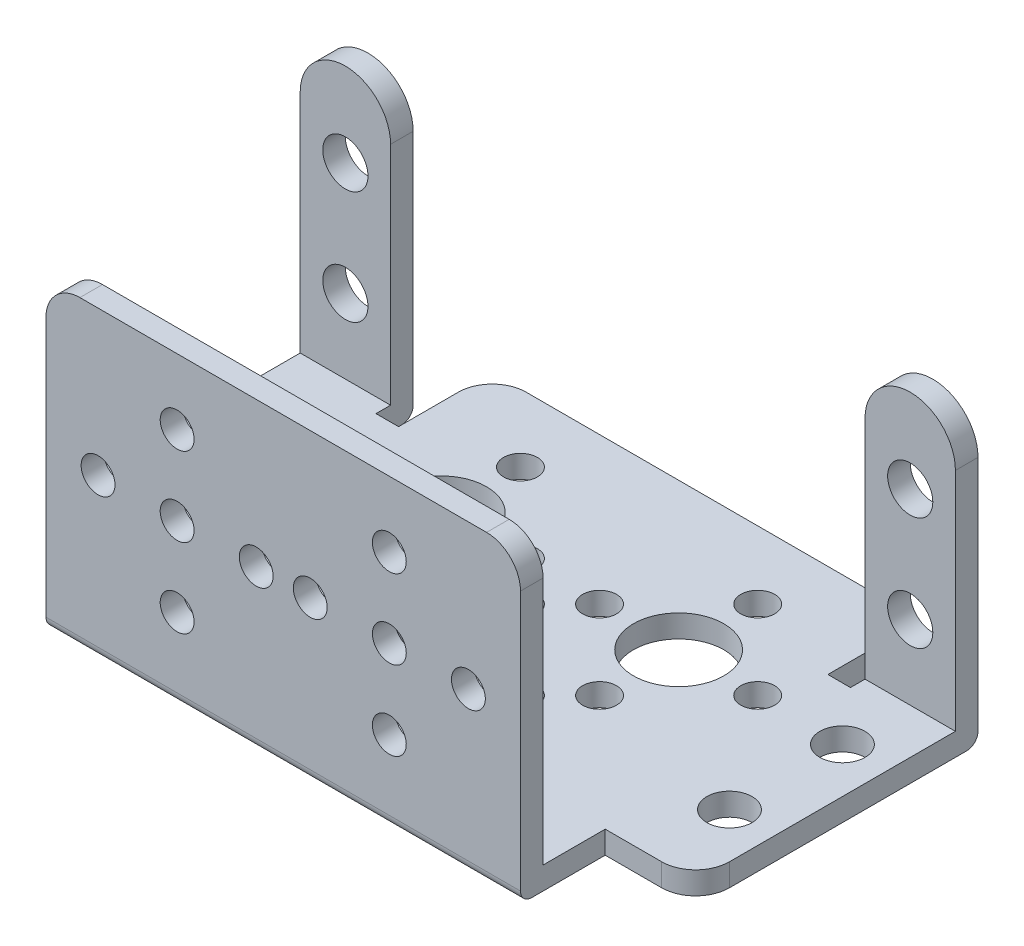
SolidWorks part; units mm, degrees
ref_plane "Front Plane" through (0, 0, 0) normal (0, 0, 1) x (1, 0, 0)
ref_plane "Top Plane" through (0, 0, 0) normal (0, 1, 0) x (1, 0, 0)
ref_plane "Right Plane" through (0, 0, 0) normal (1, 0, 0) x (0, 0, -1)
sketch "Sketch1" plane through (0, 0, 0) normal (0, 1, 0) x (1, 0, 0)
  line L0 (0, 0) -> (0, 35.8825) construction
  line L1 (21, 0) -> (-21, 0)
  line L2 (-21, 0) -> (-21, 7.5)
  line L3 (-21, 7.5) -> (-26, 7.5)
  line L4 (-29, 10.5) -> (-29, 32.5)
  line L5 (-29, 32.5) -> (-21, 32.5)
  line L6 (-21, 32.5) -> (-21, 29.2093)
  line L7 (-21, 29.2093) -> (-19, 29.2093)
  line L8 (-19, 29.2093) -> (-19, 34.5)
  line L9 (-16, 37.5) -> (16, 37.5)
  line L10 (21, 0) -> (21, 7.5)
  line L11 (21, 7.5) -> (26, 7.5)
  line L12 (19, 29.2093) -> (19, 34.5)
  line L13 (21, 29.2093) -> (19, 29.2093)
  line L14 (21, 32.5) -> (21, 29.2093)
  line L15 (29, 32.5) -> (21, 32.5)
  line L16 (29, 10.5) -> (29, 32.5)
  circle A0 centre (-25, 24.5) radius 2
  circle A1 centre (-25, 14.5) radius 2
  circle A2 centre (25, 14.5) radius 2
  circle A3 centre (25, 24.5) radius 2
  arc A4 (19, 34.5) -> (16, 37.5) centre (16, 34.5) ccw
  arc A5 (26, 7.5) -> (29, 10.5) centre (26, 10.5) ccw
  arc A6 (-19, 34.5) -> (-16, 37.5) centre (-16, 34.5) cw
  arc A7 (-26, 7.5) -> (-29, 10.5) centre (-26, 10.5) cw
  circle A8 centre (0, 14) radius 7 construction
  circle A9 centre (0, 14) radius 4
  circle A10 centre (0, 21) radius 1.5
  circle A11 centre (7, 14) radius 1.5
  circle A12 centre (0, 7) radius 1.5
  circle A13 centre (-7, 14) radius 1.5
  circle A14 centre (10.5, 24.5) radius 7 construction
  circle A15 centre (10.5, 24.5) radius 4
  circle A16 centre (10.5, 31.5) radius 1.5
  circle A20 centre (-10.5, 24.5) radius 7 construction
  circle A21 centre (-10.5, 24.5) radius 4
  circle A22 centre (-10.5, 31.5) radius 1.5
  circle A26 centre (3.5, 24.5) radius 1.5
  circle A27 centre (10.5, 17.5) radius 1.5
  circle A28 centre (17.5, 24.5) radius 1.5
  circle A29 centre (-3.5, 24.5) radius 1.5
  circle A30 centre (-10.5, 17.5) radius 1.5
  circle A31 centre (-17.5, 24.5) radius 1.5
  point P13 (0, 37.5)
  point P30 (19, 37.5)
  point P33 (29, 7.5)
  point P36 (-19, 37.5)
  point P39 (-29, 7.5)
  dimension "D6" = 4
  dimension "D7" = 4
  dimension "D8" = 10
  dimension "D9" = 14.5
  dimension "D11" = 3
  dimension "D12" = 14
  dimension "D13" = 8
  dimension "D14" = 3
  dimension "D16" = 14
  dimension "D17" = 8
  dimension "D18" = 3
  dimension "D19" = 14
  dimension "D20" = 8
  dimension "D21" = 3
  dimension "D24" = 21
  dimension "D26" = 14
  dimension "D1" = 38
  dimension "D2" = 58
  dimension "D3" = 37.5
  dimension "D4" = 32.5
  dimension "D5" = 2
  dimension "D10" = 7.5
  dimension "D25" = 10.5
  dimension "D15" = 4
  dimension "D22" = 4
  dimension "D23" = 4
extrude "Boss-Extrude1" add sketch "Sketch1" along normal blind 27
sketch "Sketch3" plane through (0, 0, 0) normal (1, 0, 0) x (0, 0, -1)
  line L0 (0, 27) -> (0, 0) construction
  line L1 (2, 28.5272) -> (30.5, 28.5272)
  line L2 (2, 28.5272) -> (2, 2)
  line L3 (2, 2) -> (30.5, 2)
  line L4 (30.5, 28.5272) -> (30.5, 2)
  line L5 (0, 0) -> (7.5, 0) construction
  line L7 (32.557, 2) -> (38.8255, 2)
  line L8 (32.557, 2) -> (32.557, 28.5272)
  line L9 (32.557, 28.5272) -> (38.8255, 28.5272)
  line L10 (38.8255, 2) -> (38.8255, 28.5272)
  dimension "D1" = 28.5
  dimension "D2" = 2
  dimension "D3" = 2
extrude "Cut-Extrude1" cut sketch "Sketch3" against normal through all both and the other way through all
sketch "Sketch4" plane through (0, 0, 0) normal (0, 0, 1) x (1, 0, 0)
  line L0 (-21, 27) -> (-21, 2) construction
  line L1 (-29, 0) -> (-21, 0) construction
  line L2 (-29, 0) -> (-29, 26) construction
  line L3 (-29, 26) -> (-21, 26) construction
  line L4 (-21, 0) -> (-21, 26) construction
  line L5 (0, 0) -> (0, 14.6606) construction
  line L6 (29, 0) -> (21, 0) construction
  line L7 (21, 0) -> (21, 26) construction
  line L8 (29, 0) -> (29, 26) construction
  line L9 (29, 26) -> (21, 26) construction
  line L10 (-29, 22) -> (-29, 28.588)
  line L11 (-29, 28.588) -> (-21, 28.588)
  line L12 (-21, 28.588) -> (-21, 22)
  line L14 (29, 26) -> (21, 26) construction
  line L16 (21, 28.588) -> (21, 22)
  line L17 (29, 28.588) -> (21, 28.588)
  line L18 (29, 22) -> (29, 28.588)
  arc A0 (-21, 22) -> (-29, 22) centre (-25, 22) ccw
  arc A1 (21, 22) -> (29, 22) centre (25, 22) cw
  circle A2 centre (-25, 18.5734) radius 2
  circle A3 centre (-25, 8.5734) radius 2
  circle A4 centre (-9.3912, 14.1874) radius 7 construction
  circle A5 centre (-9.3912, 14.1874) radius 4 construction
  circle A6 centre (-9.3912, 21.1874) radius 1.5
  circle A7 centre (-2.3912, 14.1874) radius 1.5
  circle A8 centre (-9.3912, 7.1874) radius 1.5
  circle A9 centre (-16.3912, 14.1874) radius 1.5
  circle A10 centre (2.3912, 14.1874) radius 1.5
  circle A11 centre (9.3912, 14.1874) radius 7 construction
  circle A12 centre (16.3912, 14.1874) radius 1.5
  circle A13 centre (9.3912, 7.1874) radius 1.5
  circle A14 centre (9.3912, 21.1874) radius 1.5
  circle A15 centre (9.3912, 14.1874) radius 4 construction
  circle A16 centre (25, 8.5734) radius 2
  circle A17 centre (25, 18.5734) radius 2
  circle A18 centre (-9.3912, 14.1874) radius 1.5
  circle A19 centre (9.3912, 14.1874) radius 1.5
  dimension "D2" = 4
  dimension "D3" = 4
  dimension "D4" = 10
  dimension "D5" = 14
  dimension "D6" = 4
  dimension "D7" = 3
  dimension "D8" = 3
  dimension "D1" = 26
extrude "Cut-Extrude2" cut sketch "Sketch4" against normal through all
sketch "Sketch5" plane through (0, 0, -32.557) normal (0, 0, -1) x (-1, 0, 0)
  line L1 (-19, 2) -> (19, 2)
  line L2 (-19, 2) -> (-19, 29.0641)
  line L3 (-19, 29.0641) -> (19, 29.0641)
  line L4 (19, 2) -> (19, 29.0641)
extrude "Cut-Extrude3" cut sketch "Sketch5" against normal blind 27
fillet "Fillet1" radius 3 2 edges at (21, 27, -1) (-21, 27, -1)
fillet "Fillet2" radius 1 3 edges at (-25, 0, -32.5) (25, 0, -32.5) (0, 0, 0)
